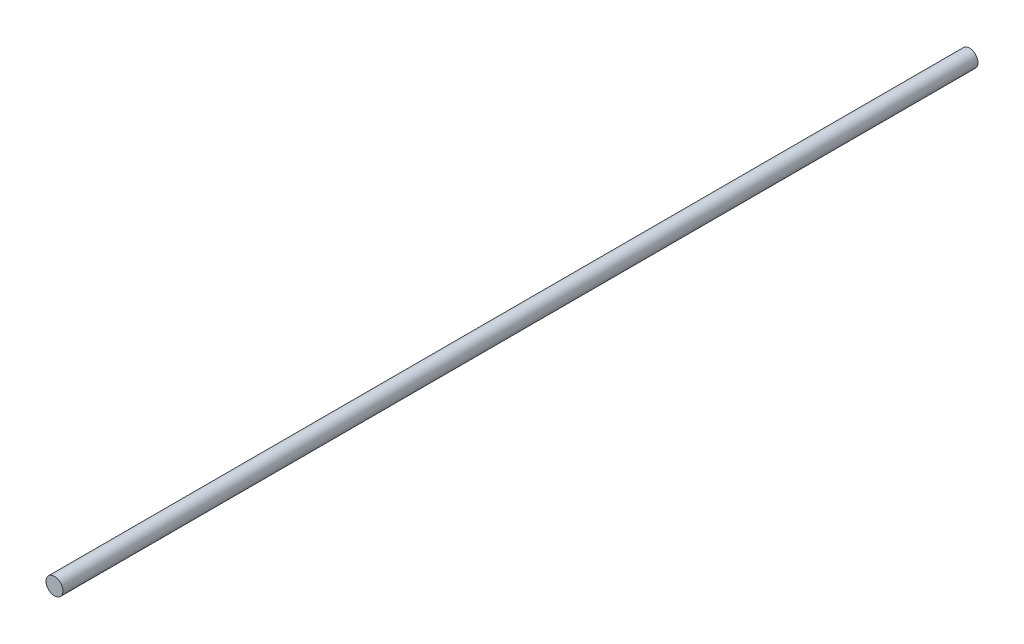
SolidWorks part; units mm, degrees
ref_plane "Front Plane" through (0, 0, 0) normal (0, 0, 1) x (1, 0, 0)
ref_plane "Top Plane" through (0, 0, 0) normal (0, 1, 0) x (1, 0, 0)
ref_plane "Right Plane" through (0, 0, 0) normal (1, 0, 0) x (0, 0, -1)
sketch "Sketch1" plane through (0, 0, 0) normal (0, 0, 1) x (1, 0, 0)
  circle A0 centre (0, 0) radius 5
extrude "Boss-Extrude1" add sketch "Sketch1" along normal blind 540
